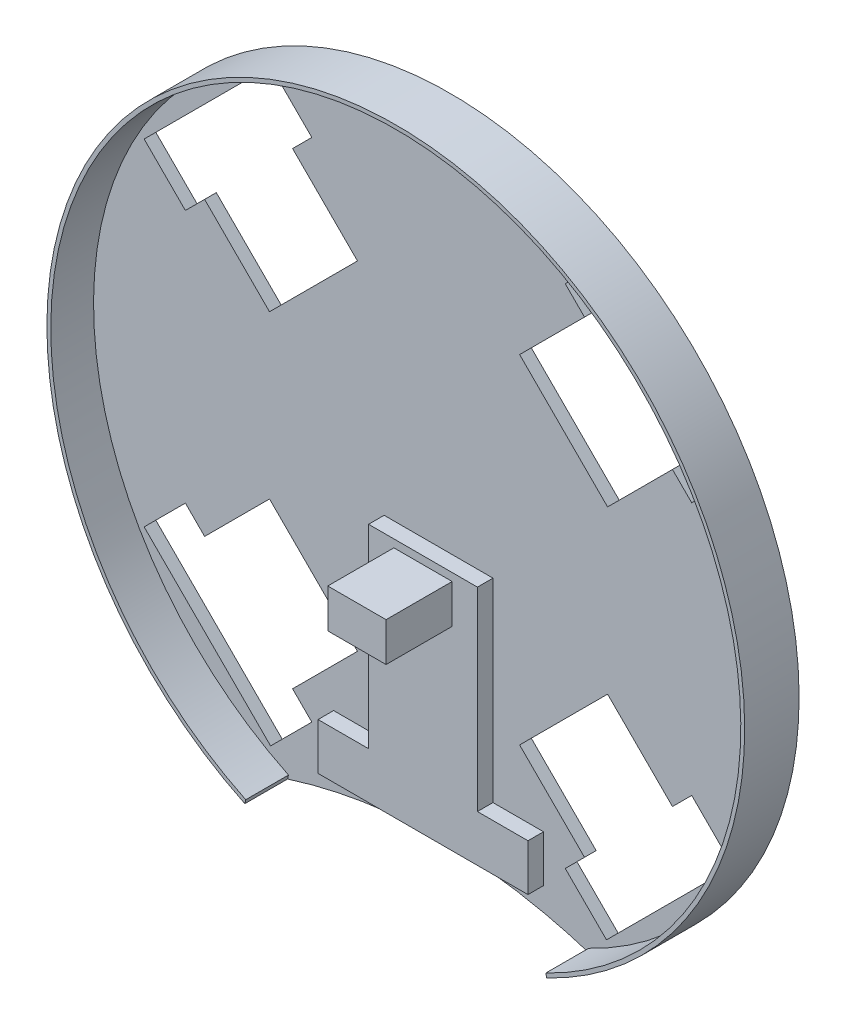
SolidWorks part; units mm, degrees
ref_plane "Front Plane" through (0, 0, 0) normal (0, 0, 1) x (1, 0, 0)
ref_plane "Top Plane" through (0, 0, 0) normal (0, 1, 0) x (1, 0, 0)
ref_plane "Right Plane" through (0, 0, 0) normal (1, 0, 0) x (0, 0, -1)
sketch "Model" plane through (0, 0, 0) normal (0, 0, 1) x (1, 0, 0)
  line L0 (-20.8549, -43.4823) -> (-37.5467, -60.1741)
  line L1 (-43.4823, -20.8549) -> (-20.8549, -43.4823)
  line L2 (-60.1741, -37.5467) -> (-43.4823, -20.8549)
  line L3 (-60.1741, -37.5467) -> (-65.1239, -32.597)
  line L4 (-65.1239, -32.597) -> (-75.7305, -43.2036)
  line L5 (-75.7305, -43.2036) -> (-43.2036, -75.7305)
  line L6 (-43.2036, -75.7305) -> (-32.597, -65.1239)
  line L7 (-32.597, -65.1239) -> (-37.5467, -60.1741)
  line L8 (43.4823, -20.8549) -> (60.1741, -37.5467)
  line L9 (20.8549, -43.4823) -> (43.4823, -20.8549)
  line L10 (37.5467, -60.1741) -> (20.8549, -43.4823)
  line L11 (37.5467, -60.1741) -> (32.597, -65.1239)
  line L12 (32.597, -65.1239) -> (43.2036, -75.7305)
  line L13 (43.2036, -75.7305) -> (75.7305, -43.2036)
  line L14 (75.7305, -43.2036) -> (65.1239, -32.597)
  line L15 (65.1239, -32.597) -> (60.1741, -37.5467)
  line L16 (20.8549, 43.4823) -> (37.5467, 60.1741)
  line L17 (43.4823, 20.8549) -> (20.8549, 43.4823)
  line L18 (60.1741, 37.5467) -> (43.4823, 20.8549)
  line L19 (60.1741, 37.5467) -> (65.1239, 32.597)
  line L20 (65.1239, 32.597) -> (75.7305, 43.2036)
  line L21 (75.7305, 43.2036) -> (43.2036, 75.7305)
  line L22 (43.2036, 75.7305) -> (32.597, 65.1239)
  line L23 (32.597, 65.1239) -> (37.5467, 60.1741)
  line L24 (-43.4823, 20.8549) -> (-60.1741, 37.5467)
  line L25 (-20.8549, 43.4823) -> (-43.4823, 20.8549)
  line L26 (-37.5467, 60.1741) -> (-20.8549, 43.4823)
  line L27 (-37.5467, 60.1741) -> (-32.597, 65.1239)
  line L28 (-32.597, 65.1239) -> (-43.2036, 75.7305)
  line L29 (-43.2036, 75.7305) -> (-75.7305, 43.2036)
  line L30 (-75.7305, 43.2036) -> (-65.1239, 32.597)
  line L31 (-65.1239, 32.597) -> (-60.1741, 37.5467)
  arc A0 (38.8292, -80.9157) -> (-38.8292, -80.9157) centre (0, 0) ccw
  spline S0 degree 3 poles (38.8292, -80.9157) (12.9431, -72.6948) (-12.9431, -72.6948) (-38.8292, -80.9157) knots 0 0 0 0 1 1 1 1
extrude "Boss-Extrude1" add sketch "Model" along normal blind 3
sketch "Sketch2" plane through (0, 0, 3) normal (0, 0, 1) x (1, 0, 0)
  line L0 (-38.8292, -80.9157) -> (38.8292, -80.9157) construction
  line L1 (-38.601, -79.9157) -> (38.601, -79.9157) construction
  line L2 (-38.8292, -80.9157) -> (-38.601, -79.9157)
  line L3 (38.8292, -80.9157) -> (38.601, -79.9157)
  arc A0 (38.8292, -80.9157) -> (-38.8292, -80.9157) centre (0, 0) ccw construction
  arc A1 (38.8292, -80.9157) -> (-38.8292, -80.9157) centre (0, 0) ccw
  arc A2 (38.601, -79.9157) -> (-38.601, -79.9157) centre (0, 0) ccw
  dimension "D1" = 1
extrude "Boss-Extrude2" add sketch "Sketch2" along normal blind 11
sketch "Sketch3" plane through (0, 0, 3) normal (0, 0, 1) x (1, 0, 0)
  line L0 (0, 0) -> (0, -34.75) construction
  line L1 (-27, -59.75) -> (27, -59.75)
  line L2 (-27, -59.75) -> (-27, -71.75)
  line L3 (-27, -71.75) -> (27, -71.75)
  line L4 (27, -59.75) -> (27, -71.75)
  line L5 (-27, -59.75) -> (27, -71.75) construction
  line L6 (-27, -71.75) -> (27, -59.75) construction
  line L7 (-14, -9.75) -> (14, -9.75)
  line L8 (-14, -9.75) -> (-14, -59.75)
  line L9 (-14, -59.75) -> (14, -59.75)
  line L10 (14, -9.75) -> (14, -59.75)
  line L11 (-14, -9.75) -> (14, -59.75) construction
  line L12 (-14, -59.75) -> (14, -9.75) construction
  line L13 (0, -34.75) -> (0, -65.75) construction
  line L14 (0, -71.75) -> (0, -74.75) construction
  parabola Q9 (-38.8292, -80.9157) -> (38.8292, -80.9157) focus (0, -135.8826) apex (0, -74.75) construction
  point P0 (0, -65.75)
  point P5 (0, -34.75)
  dimension "D1" = 54
  dimension "D2" = 12
  dimension "D3" = 3
  dimension "D4" = 50
  dimension "D5" = 28
extrude "Boss-Extrude3" add sketch "Sketch3" along normal blind 4 contours L10 L7 L8 L1 | L4 L1 L2 L3
sketch "Sketch4" plane through (0, 0, 7) normal (0, 0, 1) x (1, 0, 0)
  line L0 (0, 0) -> (0, -16.75) construction
  line L1 (-7.5, -11.75) -> (7.5, -11.75)
  line L2 (-7.5, -11.75) -> (-7.5, -21.75)
  line L3 (-7.5, -21.75) -> (7.5, -21.75)
  line L4 (7.5, -11.75) -> (7.5, -21.75)
  line L5 (-7.5, -11.75) -> (7.5, -21.75) construction
  line L6 (-7.5, -21.75) -> (7.5, -11.75) construction
  line L7 (-14, -9.75) -> (14, -9.75) construction
  point P0 (0, -16.75)
  dimension "D1" = 10
  dimension "D2" = 15
  dimension "D3" = 2
extrude "Boss-Extrude4" add sketch "Sketch4" along normal blind 17
